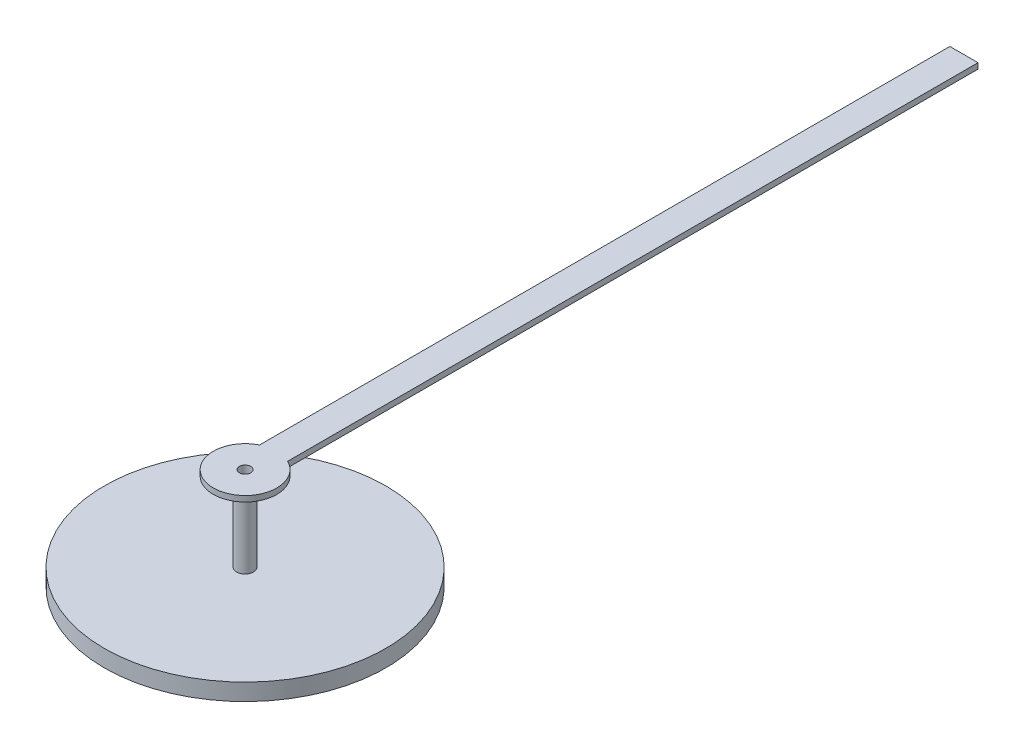
SolidWorks part; units mm, degrees
ref_plane "Front Plane" through (0, 0, 0) normal (0, 0, 1) x (1, 0, 0)
ref_plane "Top Plane" through (0, 0, 0) normal (0, 1, 0) x (1, 0, 0)
ref_plane "Right Plane" through (0, 0, 0) normal (1, 0, 0) x (0, 0, -1)
sketch "Sketch1" plane through (0, 0, 0) normal (0, 1, 0) x (1, 0, 0)
  line L1 (-2.0666, 0) -> (2.0487, 0) construction
  line L4 (-0.25, 12.7639) -> (0.25, 12.7639)
  line L5 (-0.25, 12.7639) -> (-0.25, 0.506)
  line L9 (0.25, 12.7639) -> (0.25, 0.506)
  line L12 (-0.25, 12.7639) -> (0.249, 0.5065) construction
  line L13 (-0.249, 0.5065) -> (0.25, 12.7639) construction
  arc A0 (-0.3028, 4.1713) -> (-0.0998, 5.0369) centre (-2.0997, 5.0494) ccw construction
  arc A1 (0.3028, 4.1713) -> (0.0998, 5.0369) centre (2.0997, 5.0494) cw construction
  arc A2 (-0.25, 0.506) -> (0.25, 0.506) centre (0, 0) ccw
  point P16 (0, 6.6231)
  dimension "D1" = 0.5
  dimension "D2" = 2
  dimension "D3" = 2
extrude "Boss-Extrude1" add sketch "Sketch1" along normal blind 0.1
sketch "Sketch2" plane through (0, 0.1, 0) normal (0, -1, 0) x (1, 0, 0)
  circle A0 centre (0, 0) radius 0.15
  dimension "D1" = 0.3
extrude "Boss-Extrude2" add sketch "Sketch2" along normal blind 1.5
sketch "Sketch3" plane through (0, -1.4, 0) normal (0, -1, 0) x (1, 0, 0)
  circle A0 centre (0, 0) radius 2.5
  dimension "D1" = 5
extrude "Boss-Extrude3" add sketch "Sketch3" along normal blind 0.3
sketch "Sketch4" plane through (0, 0.1, 0) normal (0, 1, 0) x (1, 0, 0)
  circle A0 centre (0, 0) radius 0.1
  dimension "D1" = 0.2
extrude "Cut-Extrude1" cut sketch "Sketch4" against normal through all
